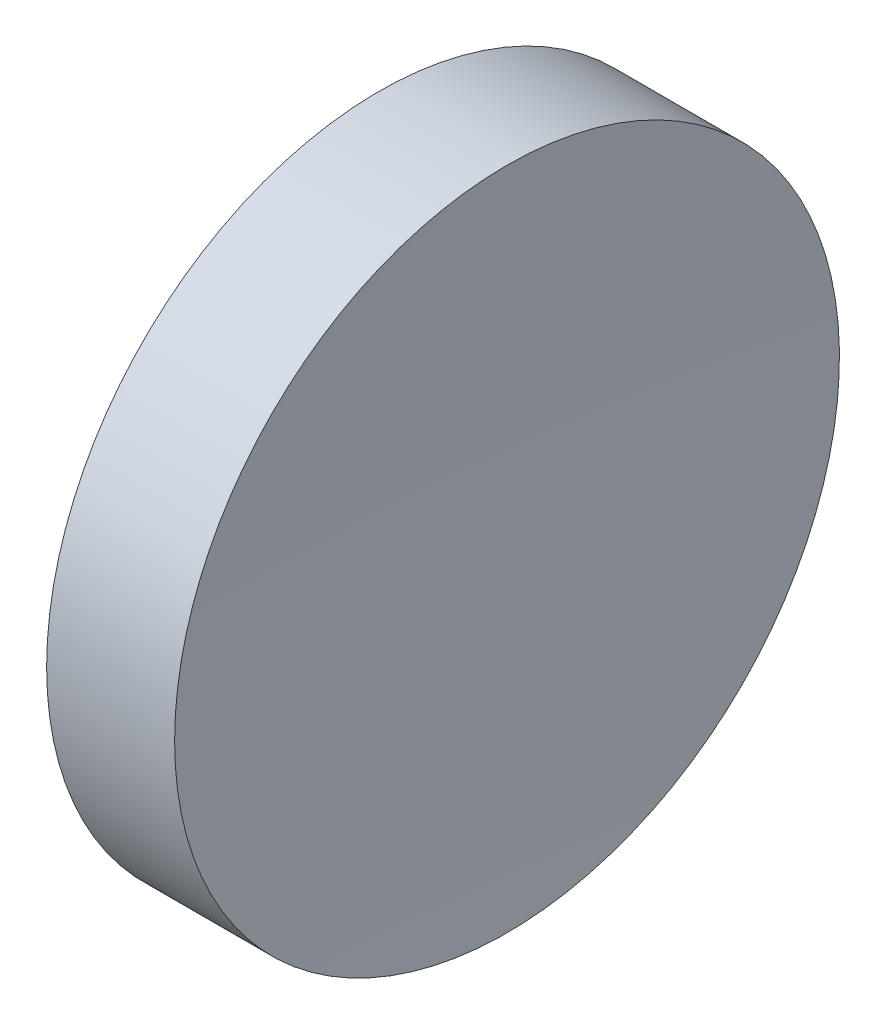
SolidWorks part; units mm, degrees
ref_plane "前视基准面" through (0, 0, 0) normal (0, 0, 1) x (1, 0, 0)
ref_plane "上视基准面" through (0, 0, 0) normal (0, 1, 0) x (1, 0, 0)
ref_plane "右视基准面" through (0, 0, 0) normal (1, 0, 0) x (0, 0, -1)
sketch "草图1" plane through (0, 0, 0) normal (0, 0, 1) x (1, 0, 0)
  line L0 (217.9703, 138.756) -> (265.5527, 138.756) construction
  line L1 (230.1853, 138.756) -> (230.1853, 163.756)
  line L2 (239.1853, 138.756) -> (230.1853, 138.756)
  line L3 (230.1853, 163.756) -> (239.8107, 163.756)
  arc A0 (239.8107, 163.756) -> (239.1853, 138.756) centre (739.1853, 138.756) ccw
  dimension "D1" = 500
  dimension "D2" = 9.6254
revolve "旋转1" add sketch "草图1" angle 360 about L0
